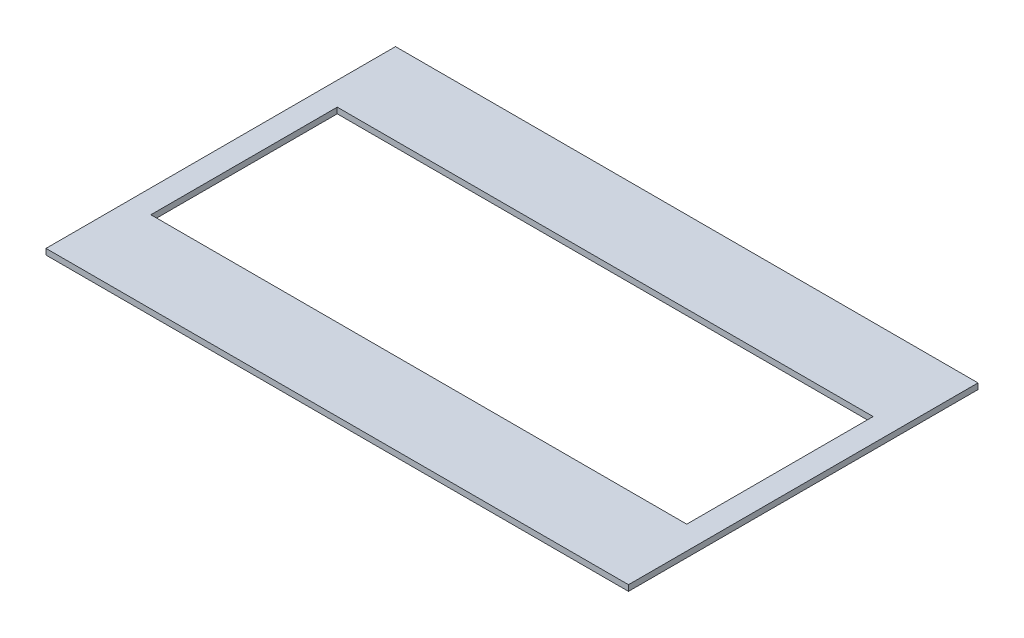
SolidWorks part; units mm, degrees
ref_plane "Front Plane" through (0, 0, 0) normal (0, 0, 1) x (1, 0, 0)
ref_plane "Top Plane" through (0, 0, 0) normal (0, 1, 0) x (1, 0, 0)
ref_plane "Right Plane" through (0, 0, 0) normal (1, 0, 0) x (0, 0, -1)
sketch "Sketch1" plane through (0, 0, 0) normal (0, 1, 0) x (1, 0, 0)
  line L0 (-250, 115) -> (250, 115) construction
  line L1 (-250, 150) -> (250, 150)
  line L2 (-250, 150) -> (-250, -150)
  line L3 (-250, -150) -> (250, -150)
  line L4 (250, 150) -> (250, -150)
  line L5 (-250, 150) -> (250, -150) construction
  line L6 (-250, -150) -> (250, 150) construction
  circle A0 centre (-220, 115) radius 3
  circle A1 centre (-200, 115) radius 3
  circle A2 centre (-180, 115) radius 3
  circle A3 centre (-160, 115) radius 3
  circle A4 centre (-140, 115) radius 3
  circle A5 centre (-120, 115) radius 3
  circle A6 centre (-100, 115) radius 3
  circle A7 centre (-80, 115) radius 3
  circle A8 centre (-60, 115) radius 3
  circle A9 centre (-40, 115) radius 3
  circle A10 centre (-20, 115) radius 3
  circle A11 centre (0, 115) radius 3
  circle A12 centre (20, 115) radius 3
  circle A13 centre (40, 115) radius 3
  circle A14 centre (60, 115) radius 3
  circle A15 centre (80, 115) radius 3
  circle A16 centre (100, 115) radius 3
  circle A17 centre (120, 115) radius 3
  circle A18 centre (140, 115) radius 3
  circle A19 centre (160, 115) radius 3
  circle A20 centre (180, 115) radius 3
  circle A21 centre (200, 115) radius 3
  circle A22 centre (220, 115) radius 3
  circle A24 centre (-220, 90) radius 3
  circle A25 centre (-200, 90) radius 3
  circle A26 centre (-180, 90) radius 3
  circle A27 centre (-160, 90) radius 3
  circle A28 centre (-140, 90) radius 3
  circle A29 centre (-120, 90) radius 3
  circle A30 centre (-100, 90) radius 3
  circle A31 centre (-80, 90) radius 3
  circle A32 centre (-60, 90) radius 3
  circle A34 centre (-40, 90) radius 3
  circle A35 centre (-20, 90) radius 3
  circle A36 centre (0, 90) radius 3
  circle A37 centre (20, 90) radius 3
  circle A38 centre (40, 90) radius 3
  circle A39 centre (60, 90) radius 3
  circle A40 centre (80, 90) radius 3
  circle A41 centre (100, 90) radius 3
  circle A42 centre (120, 90) radius 3
  circle A43 centre (140, 90) radius 3
  circle A44 centre (160, 90) radius 3
  circle A45 centre (180, 90) radius 3
  circle A46 centre (200, 90) radius 3
  circle A47 centre (220, 90) radius 3
  circle A48 centre (-220, 65) radius 3
  circle A49 centre (-200, 65) radius 3
  circle A50 centre (-180, 65) radius 3
  circle A51 centre (-160, 65) radius 3
  circle A52 centre (-140, 65) radius 3
  circle A53 centre (-120, 65) radius 3
  circle A54 centre (-100, 65) radius 3
  circle A55 centre (-80, 65) radius 3
  circle A56 centre (-60, 65) radius 3
  circle A58 centre (-40, 65) radius 3
  circle A59 centre (-20, 65) radius 3
  circle A60 centre (0, 65) radius 3
  circle A61 centre (20, 65) radius 3
  circle A62 centre (40, 65) radius 3
  circle A63 centre (60, 65) radius 3
  circle A64 centre (80, 65) radius 3
  circle A65 centre (100, 65) radius 3
  circle A66 centre (120, 65) radius 3
  circle A67 centre (140, 65) radius 3
  circle A68 centre (160, 65) radius 3
  circle A69 centre (180, 65) radius 3
  circle A70 centre (200, 65) radius 3
  circle A71 centre (220, 65) radius 3
  circle A72 centre (-220, 40) radius 3
  circle A73 centre (-200, 40) radius 3
  circle A74 centre (-180, 40) radius 3
  circle A75 centre (-160, 40) radius 3
  circle A76 centre (-140, 40) radius 3
  circle A77 centre (-120, 40) radius 3
  circle A78 centre (-100, 40) radius 3
  circle A79 centre (-80, 40) radius 3
  circle A80 centre (-60, 40) radius 3
  circle A82 centre (-40, 40) radius 3
  circle A83 centre (-20, 40) radius 3
  circle A84 centre (0, 40) radius 3
  circle A85 centre (20, 40) radius 3
  circle A86 centre (40, 40) radius 3
  circle A87 centre (60, 40) radius 3
  circle A88 centre (80, 40) radius 3
  circle A89 centre (100, 40) radius 3
  circle A90 centre (120, 40) radius 3
  circle A91 centre (140, 40) radius 3
  circle A92 centre (160, 40) radius 3
  circle A93 centre (180, 40) radius 3
  circle A94 centre (200, 40) radius 3
  circle A95 centre (220, 40) radius 3
  circle A96 centre (-220, 15) radius 3
  circle A97 centre (-200, 15) radius 3
  circle A98 centre (-180, 15) radius 3
  circle A99 centre (-160, 15) radius 3
  circle A100 centre (-140, 15) radius 3
  circle A101 centre (-120, 15) radius 3
  circle A102 centre (-100, 15) radius 3
  circle A103 centre (-80, 15) radius 3
  circle A104 centre (-60, 15) radius 3
  circle A106 centre (-40, 15) radius 3
  circle A107 centre (-20, 15) radius 3
  circle A108 centre (0, 15) radius 3
  circle A109 centre (20, 15) radius 3
  circle A110 centre (40, 15) radius 3
  circle A111 centre (60, 15) radius 3
  circle A112 centre (80, 15) radius 3
  circle A113 centre (100, 15) radius 3
  circle A114 centre (120, 15) radius 3
  circle A115 centre (140, 15) radius 3
  circle A116 centre (160, 15) radius 3
  circle A117 centre (180, 15) radius 3
  circle A118 centre (200, 15) radius 3
  circle A119 centre (220, 15) radius 3
  circle A120 centre (-220, -10) radius 3
  circle A121 centre (-200, -10) radius 3
  circle A122 centre (-180, -10) radius 3
  circle A123 centre (-160, -10) radius 3
  circle A124 centre (-140, -10) radius 3
  circle A125 centre (-120, -10) radius 3
  circle A126 centre (-100, -10) radius 3
  circle A127 centre (-80, -10) radius 3
  circle A128 centre (-60, -10) radius 3
  circle A130 centre (-40, -10) radius 3
  circle A131 centre (-20, -10) radius 3
  circle A132 centre (0, -10) radius 3
  circle A133 centre (20, -10) radius 3
  circle A134 centre (40, -10) radius 3
  circle A135 centre (60, -10) radius 3
  circle A136 centre (80, -10) radius 3
  circle A137 centre (100, -10) radius 3
  circle A138 centre (120, -10) radius 3
  circle A139 centre (140, -10) radius 3
  circle A140 centre (160, -10) radius 3
  circle A141 centre (180, -10) radius 3
  circle A142 centre (200, -10) radius 3
  circle A143 centre (220, -10) radius 3
  circle A144 centre (-220, -35) radius 3
  circle A145 centre (-200, -35) radius 3
  circle A146 centre (-180, -35) radius 3
  circle A147 centre (-160, -35) radius 3
  circle A148 centre (-140, -35) radius 3
  circle A149 centre (-120, -35) radius 3
  circle A150 centre (-100, -35) radius 3
  circle A151 centre (-80, -35) radius 3
  circle A152 centre (-60, -35) radius 3
  circle A154 centre (-40, -35) radius 3
  circle A155 centre (-20, -35) radius 3
  circle A156 centre (0, -35) radius 3
  circle A157 centre (20, -35) radius 3
  circle A158 centre (40, -35) radius 3
  circle A159 centre (60, -35) radius 3
  circle A160 centre (80, -35) radius 3
  circle A161 centre (100, -35) radius 3
  circle A162 centre (120, -35) radius 3
  circle A163 centre (140, -35) radius 3
  circle A164 centre (160, -35) radius 3
  circle A165 centre (180, -35) radius 3
  circle A166 centre (200, -35) radius 3
  circle A167 centre (220, -35) radius 3
  circle A168 centre (-220, -60) radius 3
  circle A169 centre (-200, -60) radius 3
  circle A170 centre (-180, -60) radius 3
  circle A171 centre (-160, -60) radius 3
  circle A172 centre (-140, -60) radius 3
  circle A173 centre (-120, -60) radius 3
  circle A174 centre (-100, -60) radius 3
  circle A175 centre (-80, -60) radius 3
  circle A176 centre (-60, -60) radius 3
  circle A178 centre (-40, -60) radius 3
  circle A179 centre (-20, -60) radius 3
  circle A180 centre (0, -60) radius 3
  circle A181 centre (20, -60) radius 3
  circle A182 centre (40, -60) radius 3
  circle A183 centre (60, -60) radius 3
  circle A184 centre (80, -60) radius 3
  circle A185 centre (100, -60) radius 3
  circle A186 centre (120, -60) radius 3
  circle A187 centre (140, -60) radius 3
  circle A188 centre (160, -60) radius 3
  circle A189 centre (180, -60) radius 3
  circle A190 centre (200, -60) radius 3
  circle A191 centre (220, -60) radius 3
  circle A192 centre (-220, -85) radius 3
  circle A193 centre (-200, -85) radius 3
  circle A194 centre (-180, -85) radius 3
  circle A195 centre (-160, -85) radius 3
  circle A196 centre (-140, -85) radius 3
  circle A197 centre (-120, -85) radius 3
  circle A198 centre (-100, -85) radius 3
  circle A199 centre (-80, -85) radius 3
  circle A200 centre (-60, -85) radius 3
  circle A202 centre (-40, -85) radius 3
  circle A203 centre (-20, -85) radius 3
  circle A204 centre (0, -85) radius 3
  circle A205 centre (20, -85) radius 3
  circle A206 centre (40, -85) radius 3
  circle A207 centre (60, -85) radius 3
  circle A208 centre (80, -85) radius 3
  circle A209 centre (100, -85) radius 3
  circle A210 centre (120, -85) radius 3
  circle A211 centre (140, -85) radius 3
  circle A212 centre (160, -85) radius 3
  circle A213 centre (180, -85) radius 3
  circle A214 centre (200, -85) radius 3
  circle A215 centre (220, -85) radius 3
  circle A216 centre (-220, -110) radius 3
  circle A217 centre (-200, -110) radius 3
  circle A218 centre (-180, -110) radius 3
  circle A219 centre (-160, -110) radius 3
  circle A220 centre (-140, -110) radius 3
  circle A221 centre (-120, -110) radius 3
  circle A222 centre (-100, -110) radius 3
  circle A223 centre (-80, -110) radius 3
  circle A224 centre (-60, -110) radius 3
  circle A226 centre (-40, -110) radius 3
  circle A227 centre (-20, -110) radius 3
  circle A228 centre (0, -110) radius 3
  circle A229 centre (20, -110) radius 3
  circle A230 centre (40, -110) radius 3
  circle A231 centre (60, -110) radius 3
  circle A232 centre (80, -110) radius 3
  circle A233 centre (100, -110) radius 3
  circle A234 centre (120, -110) radius 3
  circle A235 centre (140, -110) radius 3
  circle A236 centre (160, -110) radius 3
  circle A237 centre (180, -110) radius 3
  circle A238 centre (200, -110) radius 3
  circle A239 centre (220, -110) radius 3
  circle A264 centre (-220, -135) radius 3 [skipped]
  circle A265 centre (-200, -135) radius 3 [skipped]
  circle A266 centre (-180, -135) radius 3 [skipped]
  circle A267 centre (-160, -135) radius 3 [skipped]
  circle A268 centre (-140, -135) radius 3 [skipped]
  circle A269 centre (-120, -135) radius 3 [skipped]
  circle A270 centre (-100, -135) radius 3 [skipped]
  circle A271 centre (-80, -135) radius 3 [skipped]
  circle A272 centre (-60, -135) radius 3 [skipped]
  circle A273 centre (-40, -135) radius 3 [skipped]
  circle A274 centre (-20, -135) radius 3 [skipped]
  circle A275 centre (0, -135) radius 3 [skipped]
  circle A276 centre (20, -135) radius 3 [skipped]
  circle A277 centre (40, -135) radius 3 [skipped]
  circle A278 centre (60, -135) radius 3 [skipped]
  circle A279 centre (80, -135) radius 3 [skipped]
  circle A280 centre (100, -135) radius 3 [skipped]
  circle A281 centre (120, -135) radius 3 [skipped]
  circle A282 centre (140, -135) radius 3 [skipped]
  circle A283 centre (160, -135) radius 3 [skipped]
  circle A284 centre (180, -135) radius 3 [skipped]
  circle A285 centre (200, -135) radius 3 [skipped]
  circle A286 centre (220, -135) radius 3 [skipped]
  circle A297 centre (240, 115) radius 3 [skipped]
  point P0 (0, 0)
  dimension "D5" = 6
  dimension "D1" = 500
  dimension "D2" = 300
  dimension "D3" = 35
  dimension "D4" = 30
  dimension "D6" = 24
  dimension "D7" = 11
extrude "Boss-Extrude1" add sketch "Sketch1" along normal blind 5 contours L2 L1 L4 L3
sketch "Sketch2" plane through (0, 5, 0) normal (0, 1, 0) x (1, 0, 0)
  line L1 (-230, 80) -> (230, 80)
  line L2 (-230, 80) -> (-230, -80)
  line L3 (-230, -80) -> (230, -80)
  line L4 (230, 80) -> (230, -80)
  line L5 (-230, 80) -> (230, -80) construction
  line L6 (-230, -80) -> (230, 80) construction
  point P0 (0, 0)
  dimension "D1" = 460
  dimension "D2" = 160
extrude "Cut-Extrude1" cut sketch "Sketch2" against normal blind 10
